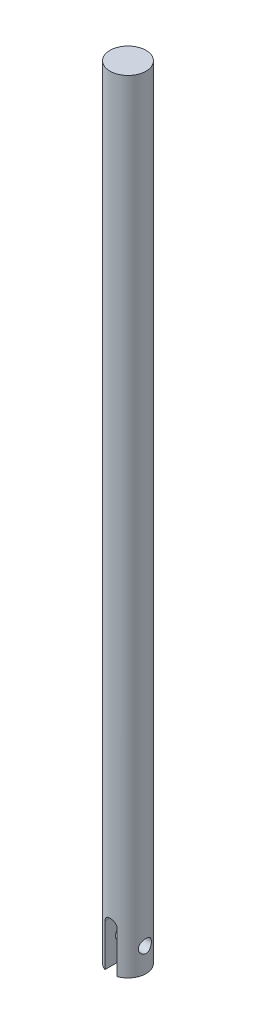
SolidWorks part; units mm, degrees
ref_plane "Front" through (0, 0, 0) normal (0, 0, 1) x (1, 0, 0)
ref_plane "Top" through (0, 0, 0) normal (0, 1, 0) x (1, 0, 0)
ref_plane "Right" through (0, 0, 0) normal (1, 0, 0) x (0, 0, -1)
sketch "Sketch1" plane through (0, 0, 0) normal (0, 1, 0) x (1, 0, 0)
  circle A0 centre (0, 0) radius 4.7625
  dimension "D1" = 9.525
extrude "Boss-Extrude1" add sketch "Sketch1" along normal blind 206.375
sketch "Sketch2" plane through (0, 0, 0) normal (0, 0, 1) x (1, 0, 0)
  line L0 (0, -11.1125) -> (0, 11.1125) construction
  line L1 (-1.5875, -11.1125) -> (-1.5875, 11.1125)
  line L2 (1.5875, -11.1125) -> (1.5875, 11.1125)
  line L3 (-4.7625, 0) -> (4.7625, 0) construction
  arc A0 (-1.5875, -11.1125) -> (1.5875, -11.1125) centre (0, -11.1125) ccw
  arc A1 (1.5875, 11.1125) -> (-1.5875, 11.1125) centre (0, 11.1125) ccw
  point P2 (0, 0)
  point P10 (0, 12.7)
  dimension "D1" = 12.7
  dimension "D2" = 3.175
extrude "Cut-Extrude1" cut sketch "Sketch2" against normal through all both and the other way through all
ref_plane "Plane1" through (4.7625, 0, 0) normal (1, 0, 0) x (0, 0, -1)
hole_wizard "#8-32 Tapped Hole1" positions "Sketch5" profile "Sketch7" tap size "#8-32" standard "ANSI Inch" end condition through all
sketch "Sketch5" plane through (4.7625, 0, 0) normal (1, 0, 0) x (0, 0, -1)
  line L0 (-4.4901, 0) -> (4.4901, 0) construction
  point P0 (0, 6.35)
  point P6 (0, 0)
  dimension "D1" = 6.35
sketch "Sketch7" plane through (4.7625, 6.35, 0) normal (0, 1, 0) x (0, 0, -1)
  line L0 (0, 0) -> (0, 9.525)
  line L1 (0, 9.525) -> (1.7272, 9.525)
  line L2 (1.7272, 9.525) -> (1.7272, 0)
  line L5 (1.7272, 0) -> (0, 0)
  line L11 (0, -6.35) -> (0, 107.95) construction
  dimension "Thru Tap Drill Dia." = 3.4544
  dimension "Thru Tap Drill Depth" = 9.525
cosmetic thread "Hole Thread1" parameters "D2"=4.1656
ref_plane "Plane2" through (0, 0, -4.7625) normal (0, 0, -1) x (-1, 0, 0)
